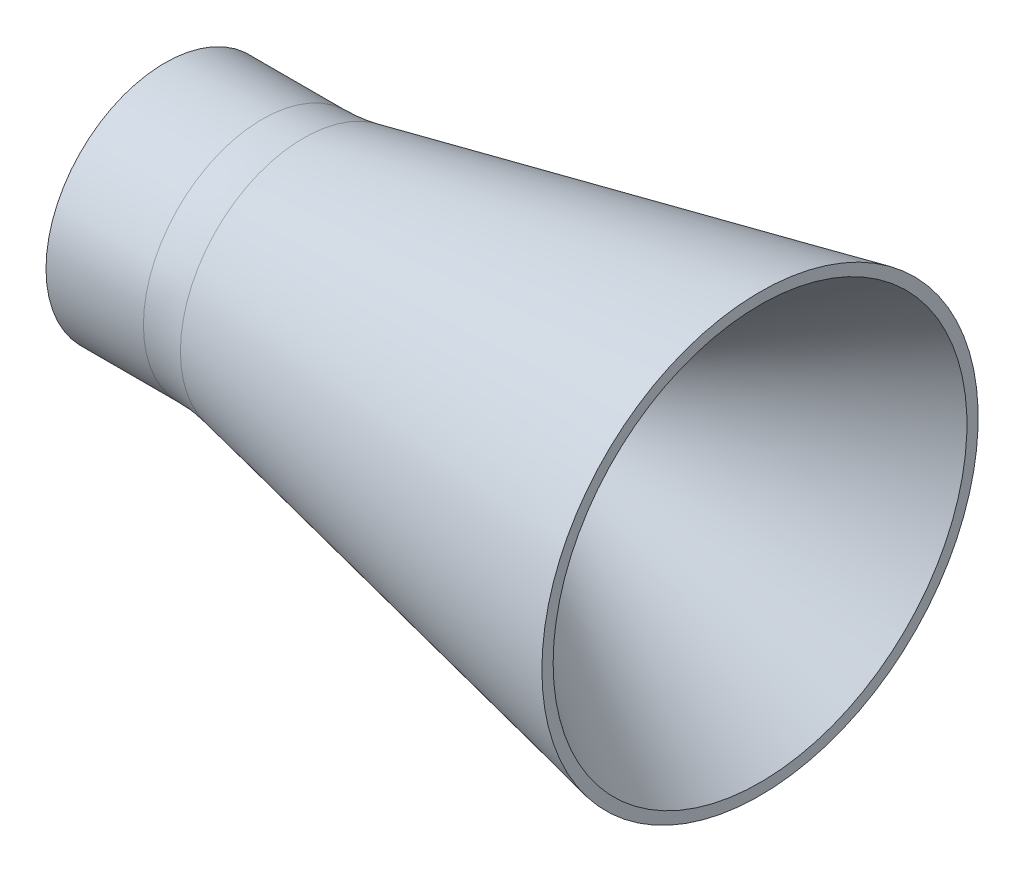
SolidWorks part; units mm, degrees
ref_plane "Front Plane" through (0, 0, 0) normal (0, 0, 1) x (1, 0, 0)
ref_plane "Top Plane" through (0, 0, 0) normal (0, 1, 0) x (1, 0, 0)
ref_plane "Right Plane" through (0, 0, 0) normal (1, 0, 0) x (0, 0, -1)
sketch "Sketch1" plane through (0, 0, 0) normal (0, 0, 1) x (1, 0, 0)
  line L0 (45.6392, 28.2986) -> (95.7463, 9.0643)
  line L1 (110.0811, 6.4075) -> (140.0811, 6.4075)
  line L5 (110.0811, 6.4075) -> (127.8518, 6.4075)
  line L6 (150.2195, 13.246) -> (246.8022, 78.3918)
  line L7 (-9.079, -13.5925) -> (413.265, -13.5925) construction
  line L8 (43.8766, 41.1639) -> (246.8022, 83.3918)
  line L9 (246.8022, 78.3918) -> (246.8022, 83.3918)
  line L10 (13.386, 34.2764) -> (-17.7706, 34.2764)
  line L12 (25.5408, 39.2764) -> (-17.7706, 39.2764)
  line L13 (-17.7706, 34.2764) -> (-17.7706, 39.2764)
  arc A0 (45.6392, 28.2986) -> (13.386, 34.2764) centre (13.386, -55.7236) ccw
  arc A1 (43.8766, 41.1639) -> (25.5408, 39.2764) centre (25.5408, 129.2764) cw
  arc A2 (127.8518, 6.4075) -> (150.2195, 13.246) centre (127.8518, 46.4075) ccw
  arc A3 (95.7463, 9.0643) -> (110.0811, 6.4075) centre (110.0811, 46.4075) ccw
  dimension "D2" = 90
  dimension "D7" = 40
  dimension "D1" = 5
  dimension "D3" = 159
  dimension "D4" = 5
  dimension "D5" = 146
  dimension "D6" = 30
  dimension "D8" = 20
revolve "Revolve2" add sketch "Sketch1" angle 360 about L7
